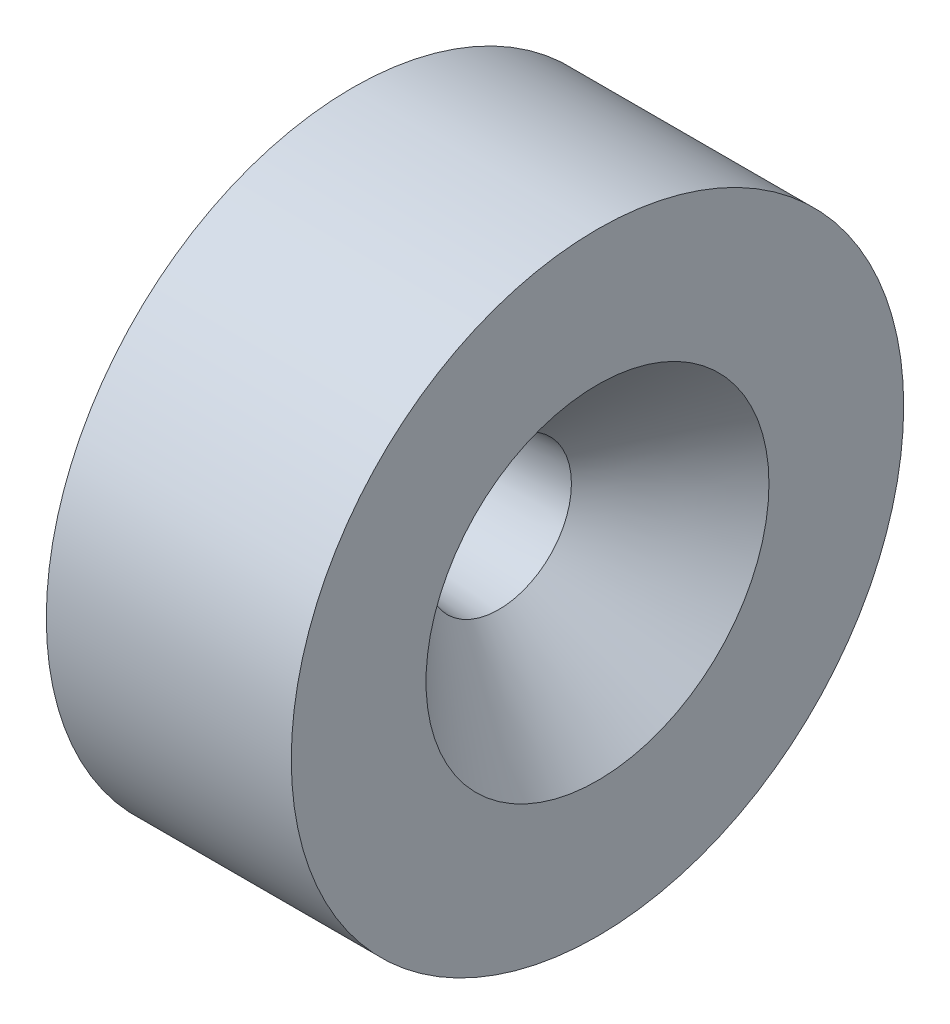
SolidWorks part; units mm, degrees
ref_plane "前视基准面" through (0, 0, 0) normal (0, 0, 1) x (1, 0, 0)
ref_plane "上视基准面" through (0, 0, 0) normal (0, 1, 0) x (1, 0, 0)
ref_plane "右视基准面" through (0, 0, 0) normal (1, 0, 0) x (0, 0, -1)
other "Configuration Table"
sketch "草图1" plane through (0, 0, 0) normal (1, 0, 0) x (0, 0, -1)
  circle A0 centre (-9.3254, -21.6999) radius 5
  dimension "D1" = 10
extrude "凸台-拉伸1" add sketch "草图1" along normal blind 4
sketch "草图2" plane through (4, 0, 0) normal (1, 0, 0) x (0, 0, -1)
  circle A0 centre (-9.3254, -21.6999) radius 1.3
  dimension "D1" = 2.6
extrude "切除-拉伸1" cut sketch "草图2" against normal through all draft 4
chamfer "倒角1" distance 1.5 angle 45 1 edges at (4, -21.6999, 8.0254)
